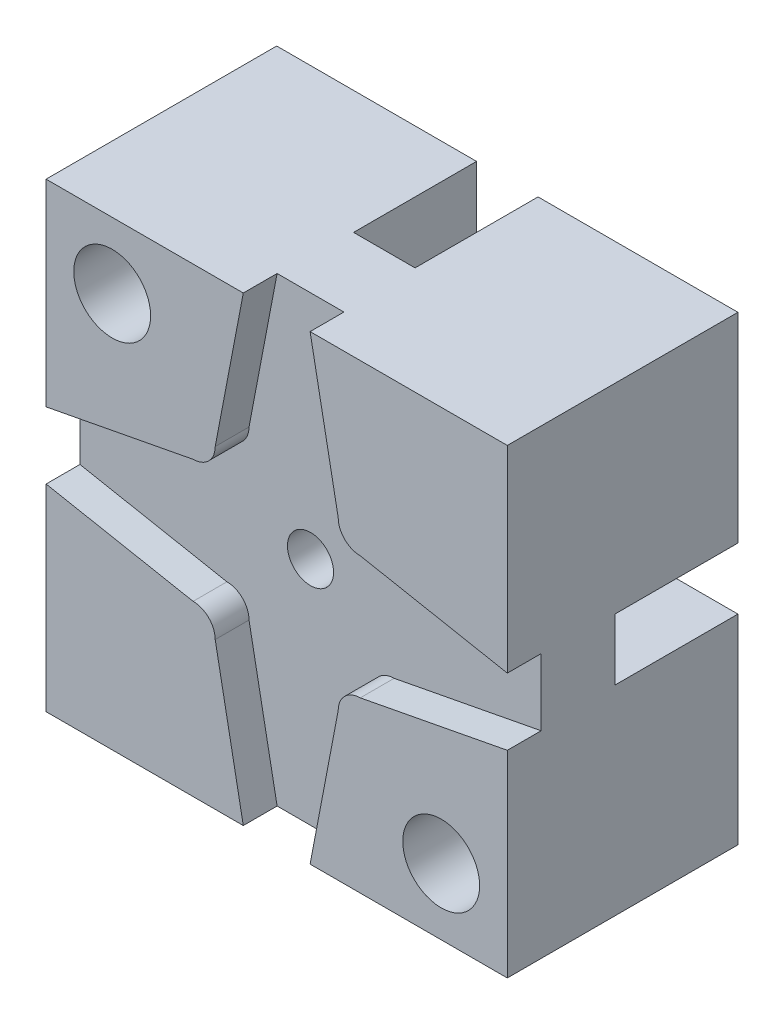
SolidWorks part; units mm, degrees
ref_plane "Front Plane" through (0, 0, 0) normal (0, 0, 1) x (1, 0, 0)
ref_plane "Top Plane" through (0, 0, 0) normal (0, 1, 0) x (1, 0, 0)
ref_plane "Right Plane" through (0, 0, 0) normal (1, 0, 0) x (0, 0, -1)
sketch "Sketch1" plane through (0, 0, 0) normal (0, 0, 1) x (1, 0, 0)
  line L1 (-15, -15) -> (15, -15)
  line L2 (-15, -15) -> (-15, 15)
  line L3 (-15, 15) -> (15, 15)
  line L4 (15, -15) -> (15, 15)
  line L5 (-15, -15) -> (15, 15) construction
  line L6 (-15, 15) -> (15, -15) construction
  point P0 (0, 0)
  dimension "D1" = 30
extrude "Boss-Extrude1" add sketch "Sketch1" along normal blind 15
sketch "Sketch2" plane through (0, 0, 15) normal (0, 0, 1) x (1, 0, 0)
  line L0 (-2, 15) -> (2, 15)
  line L1 (15, 15) -> (-15, 15) construction
  line L2 (2, 15) -> (2, 10.8167)
  line L3 (-2, 15) -> (-2, 10.8167)
  line L4 (15, 2) -> (15, -2)
  line L5 (15, -15) -> (15, 15) construction
  line L6 (15, -2) -> (10.8167, -2)
  line L7 (15, 2) -> (10.8167, 2)
  line L8 (-2, -15) -> (2, -15)
  line L9 (-15, -15) -> (15, -15) construction
  line L10 (2, -15) -> (2, -10.8167)
  line L11 (-2, -15) -> (-2, -10.8167)
  line L12 (-15, -2) -> (-15, 2)
  line L13 (-15, 15) -> (-15, -15) construction
  line L14 (-15, 2) -> (-10.8167, 2)
  line L15 (-15, -2) -> (-10.8167, -2)
  arc A0 (-10.8167, 2) -> (-10.8167, -2) centre (0, 0) ccw
  arc A1 (2, 10.8167) -> (-2, 10.8167) centre (0, 0) ccw
  arc A2 (10.8167, -2) -> (10.8167, 2) centre (0, 0) ccw
  arc A3 (-2, -10.8167) -> (2, -10.8167) centre (0, 0) ccw
  point P25 (-15, 0)
  point P28 (15, 0)
  point P29 (0, -15)
  point P30 (0, 15)
  dimension "D1" = 22
  dimension "D2" = 4
extrude "Cut-Extrude1" cut sketch "Sketch2" against normal blind 15
sketch "Sketch3" plane through (0, 0, 15) normal (0, 0, 1) x (1, 0, 0)
  line L0 (-15, 15) -> (-15, 2) construction
  line L1 (-2, 15) -> (-15, 15) construction
  line L2 (15, -15) -> (15, -2) construction
  line L3 (2, -15) -> (15, -15) construction
  circle A0 centre (-10.7, 10.7) radius 2.5
  circle A1 centre (10.7, -10.7) radius 2.5
  dimension "D1" = 5
  dimension "D6" = 5
  dimension "D2" = 4.3
  dimension "D3" = 4.3
  dimension "D4" = 4.3
  dimension "D5" = 4.3
extrude "Cut-Extrude2" cut sketch "Sketch3" against normal blind 15
sketch "Sketch4" plane through (15, 0, 0) normal (1, 0, 0) x (0, 0, -1)
  line L0 (0, -2) -> (-15, -2) construction
  line L1 (-15, 2) -> (-8, 2)
  line L2 (-15, 2) -> (-15, -2)
  line L3 (-15, -2) -> (-8, -2)
  line L4 (-8, 2) -> (-8, -2)
  line L5 (0, -2) -> (0, 2) construction
  dimension "D1" = 8
extrude "Boss-Extrude2" add sketch "Sketch4" against normal up to surface (30 mm away) up to face at (-15, 8.5, 7.5)
sketch "Sketch5" plane through (0, -15, 0) normal (0, -1, 0) x (1, 0, 0)
  line L0 (-2, 0) -> (-2, 15) construction
  line L1 (2, 15) -> (-2, 15)
  line L2 (2, 15) -> (2, 8)
  line L3 (2, 8) -> (-2, 8)
  line L4 (-2, 15) -> (-2, 8)
  line L5 (2, 0) -> (15, 0) construction
  dimension "D1" = 8
extrude "Boss-Extrude3" add sketch "Sketch5" against normal up to surface (30 mm away) up to face at (8.5, 15, 7.5)
sketch "Sketch6" plane through (0, 0, 15) normal (0, 0, 1) x (1, 0, 0)
  line L0 (-4, 5.4371) -> (-2.173, 15)
  line L3 (4, 5.4371) -> (2.173, 15)
  line L5 (2.173, 15) -> (-2.173, 15)
  line L6 (5.4371, 4) -> (15, 2.173)
  line L9 (5.4371, -4) -> (15, -2.173)
  line L11 (15, -2.173) -> (15, 2.173)
  line L12 (2.173, -15) -> (4, -5.4371)
  line L15 (-4, -5.4371) -> (-2.173, -15)
  line L17 (-2.173, -15) -> (2.173, -15)
  line L18 (-5.4371, -4) -> (-15, -2.173)
  line L21 (-5.4371, 4) -> (-15, 2.173)
  line L23 (-15, 2.173) -> (-15, -2.173)
  arc A1 (5.4371, 4) -> (4, 5.4371) centre (5.4371, 5.4371) cw
  arc A2 (5.4371, -4) -> (4, -5.4371) centre (5.4371, -5.4371) ccw
  arc A4 (-5.4371, -4) -> (-4, -5.4371) centre (-5.4371, -5.4371) cw
  arc A6 (-5.4371, 4) -> (-4, 5.4371) centre (-5.4371, 5.4371) ccw
extrude "Cut-Extrude3" cut sketch "Sketch6" against normal blind 2.2
sketch "Sketch7" plane through (0, 0, 15) normal (0, 0, 1) x (1, 0, 0)
  circle A0 centre (0, 0) radius 1.5
extrude "Cut-Extrude4" cut sketch "Sketch7" against normal blind 4.5
